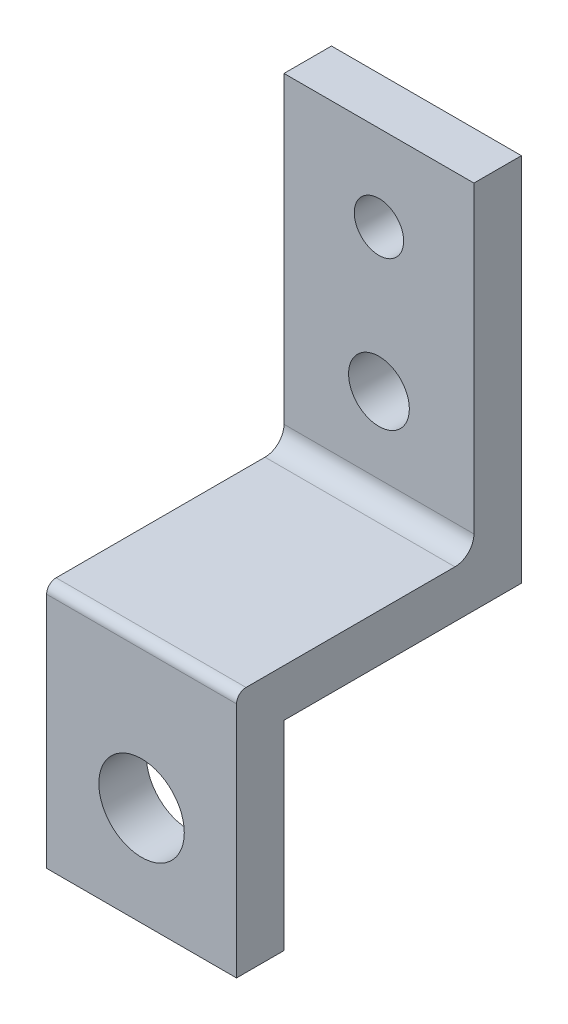
SolidWorks part; units mm, degrees
material "6061 Alloy"
ref_plane "前视基准面" through (0, 0, 0) normal (0, 0, 1) x (1, 0, 0)
ref_plane "上视基准面" through (0, 0, 0) normal (0, 1, 0) x (1, 0, 0)
ref_plane "右视基准面" through (0, 0, 0) normal (1, 0, 0) x (0, 0, -1)
other "Configuration Table"
sketch "Sketch1" plane through (0, 0, 0) normal (0, 0, 1) x (1, 0, 0)
  line L0 (0, 0) -> (0, 25) construction
  line L2 (-10, 10) -> (-10, -10)
  line L4 (10, 10) -> (10, -10)
  line L5 (-10, 10) -> (10, -10) construction
  line L6 (-10, -10) -> (10, 10) construction
  line L7 (0, 25) -> (0, 40) construction
  line L8 (0, 40) -> (0, 44) construction
  line L9 (10, 44) -> (-10, 44)
  line L10 (-10, 44) -> (-10, 10)
  line L11 (10, 44) -> (10, 10)
  line L12 (-10, -10) -> (-10, -11)
  line L13 (-10, -11) -> (10, -11)
  line L14 (10, -11) -> (10, -10)
  line L15 (0, 0) -> (0, -0.5) construction
  circle A0 centre (0, 0) radius 4.5 construction
  circle A1 centre (0, 25) radius 3 construction
  circle A2 centre (0, 40) radius 2.5 construction
  circle A3 centre (0, -0.5) radius 4.5
  dimension "D1" = 20
  dimension "D3" = 9
  dimension "D5" = 6
  dimension "D7" = 5
  dimension "D10" = 0.5
  dimension "D2" = 20
  dimension "D4" = 25
  dimension "D6" = 15
  dimension "D8" = 4
  dimension "D9" = 1
extrude "Boss-Extrude1" add sketch "Sketch1" along normal blind 5
sketch "Sketch2" plane through (0, 0, 0) normal (0, 0, -1) x (-1, 0, 0)
  line L1 (-10, -10) -> (10, -10) construction
  line L2 (-10, -10) -> (-10, 10) construction
  line L3 (-10, 10) -> (10, 10) construction
  line L4 (10, -10) -> (10, 10) construction
  line L5 (-10, -10) -> (10, 10) construction
  line L6 (-10, 10) -> (10, -10) construction
  line L7 (-10, 49) -> (10, 49)
  line L8 (-10, 49) -> (-10, 10)
  line L9 (-10, 10) -> (10, 10)
  line L10 (10, 49) -> (10, 10)
  point P0 (0, 0)
  dimension "D1" = 20
  dimension "D2" = 20
extrude "Boss-Extrude2" add sketch "Sketch2" along normal blind 25
sketch "Sketch3" plane through (10, 0, 0) normal (1, 0, 0) x (0, 0, -1)
  line L0 (0, 10) -> (0, 15) construction
  line L1 (0, 15) -> (-5, 15)
  line L2 (-5, -11) -> (-5, 44) construction
  line L7 (20, 15) -> (0, 15)
  line L8 (20, 15) -> (20, 49)
  line L9 (25, 49) -> (0, 49) construction
  line L10 (20, 49) -> (-5, 49)
  line L11 (-5, 49) -> (-5, 15)
  dimension "D1" = 5
extrude "Cut-Extrude1" cut sketch "Sketch3" against normal blind 30
mirror "Mirror1" [suppressed]
delete or keep bodies "Body-Delete/Keep 1" [suppressed] type delete bodies bodies 109
sketch "Sketch4" plane through (0, 0, -20) normal (0, 0, 1) x (1, 0, 0)
  line L0 (0, 49) -> (0, 40) construction
  line L1 (-10, 49) -> (10, 49) construction
  line L2 (0, 40) -> (0, 25) construction
  circle A0 centre (0, 40) radius 2.6
  circle A1 centre (0, 25) radius 3.2
  dimension "D1" = 9
  dimension "D2" = 15
extrude "Cut-Extrude2" cut sketch "Sketch4" against normal blind 10
fillet "Fillet1" radius 2 1 edges at (0, 15, -20)
fillet "Fillet2" radius 1 1 edges at (0, 15, 5)
